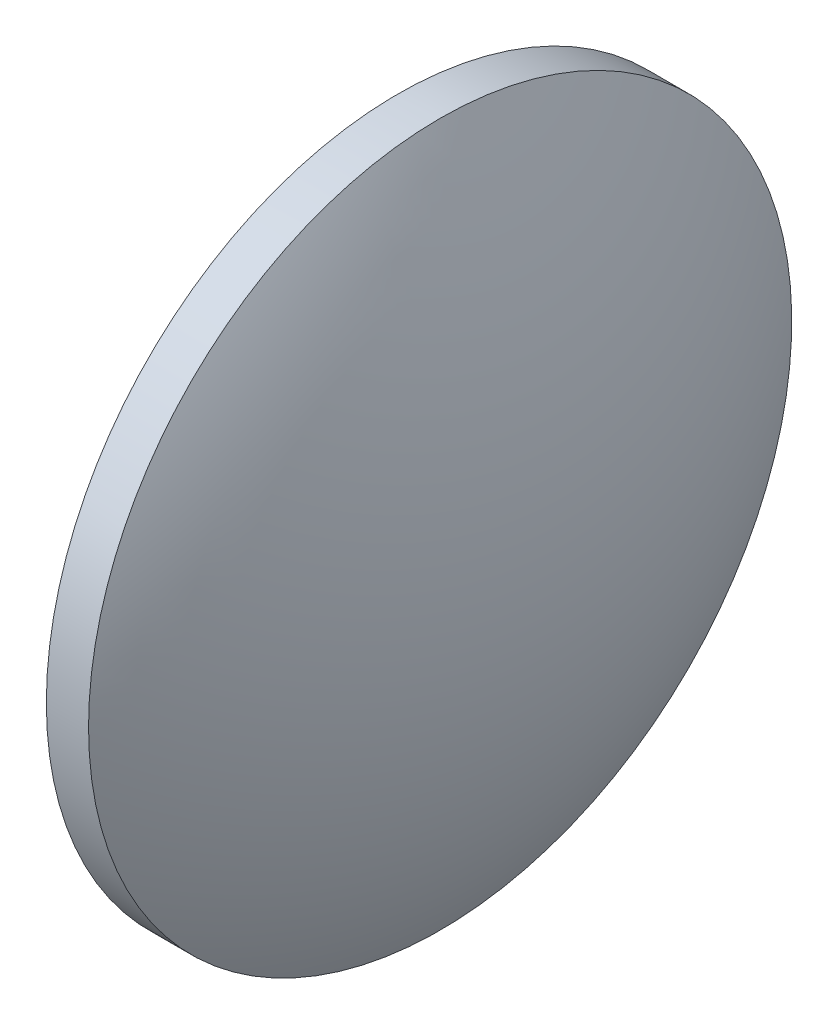
SolidWorks part; units mm, degrees
ref_plane "前视基准面" through (0, 0, 0) normal (0, 0, 1) x (1, 0, 0)
ref_plane "上视基准面" through (0, 0, 0) normal (0, 1, 0) x (1, 0, 0)
ref_plane "右视基准面" through (0, 0, 0) normal (1, 0, 0) x (0, 0, -1)
sketch "草图1" plane through (0, 0, 0) normal (0, 0, 1) x (1, 0, 0)
  line L0 (339.3127, 9.6326) -> (361.2888, 9.6326) construction
  line L1 (343.2845, 9.6326) -> (343.2845, 34.6326)
  line L2 (343.2845, 34.6326) -> (346.2845, 34.6326)
  line L3 (352.7345, 9.6326) -> (343.2845, 9.6326)
  arc A0 (352.7345, 9.6326) -> (346.2845, 34.6326) centre (301.0599, 9.6326) ccw
revolve "旋转1" add sketch "草图1" angle 360 about L0
